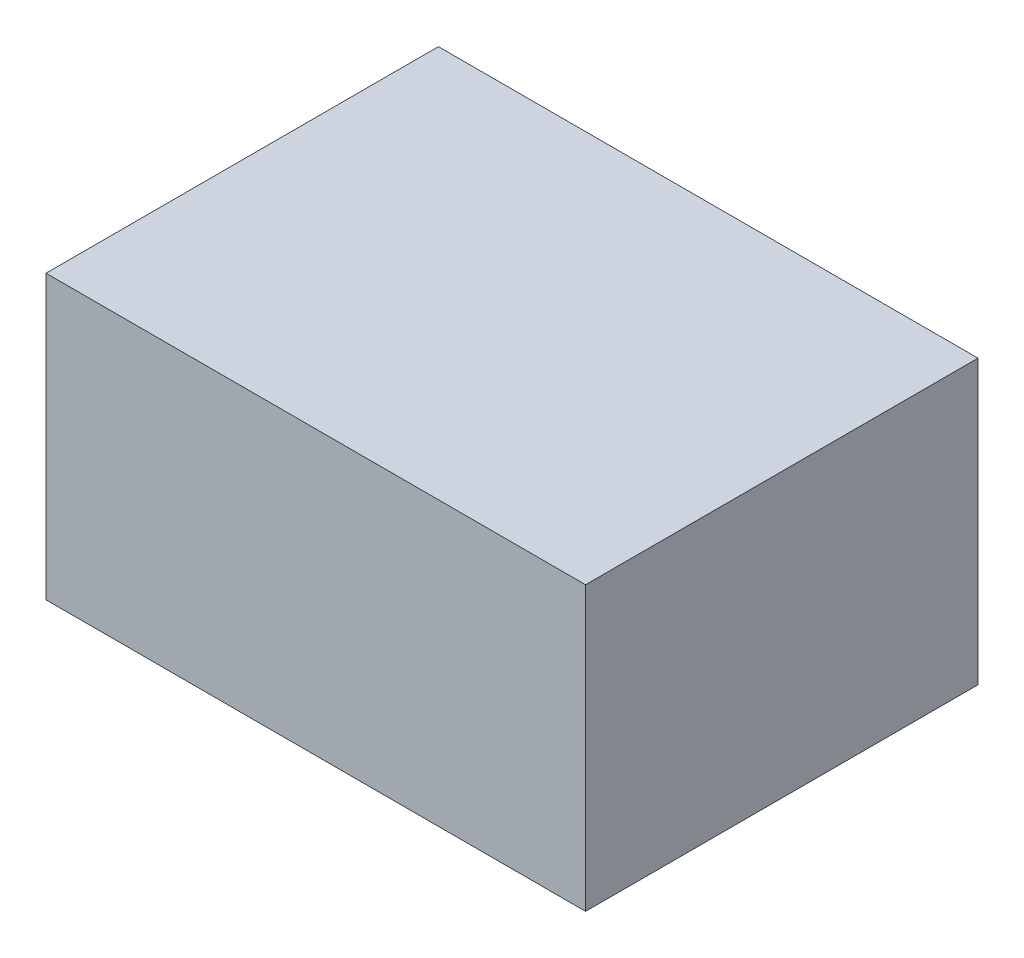
SolidWorks part; units mm, degrees
ref_plane "Plan de face" through (0, 0, 0) normal (0, 0, 1) x (1, 0, 0)
ref_plane "Plan de dessus" through (0, 0, 0) normal (0, 1, 0) x (1, 0, 0)
ref_plane "Plan de droite" through (0, 0, 0) normal (1, 0, 0) x (0, 0, -1)
sketch "Esquisse1" plane through (0, 0, 0) normal (0, 0, 1) x (1, 0, 0)
  line L1 (0, 0) -> (330, 0)
  line L2 (0, 0) -> (0, 173)
  line L3 (0, 173) -> (330, 173)
  line L4 (330, 0) -> (330, 173)
  dimension "D1" = 330
  dimension "D2" = 173
extrude "Boss.-Extru.1" add sketch "Esquisse1" along normal blind 240
